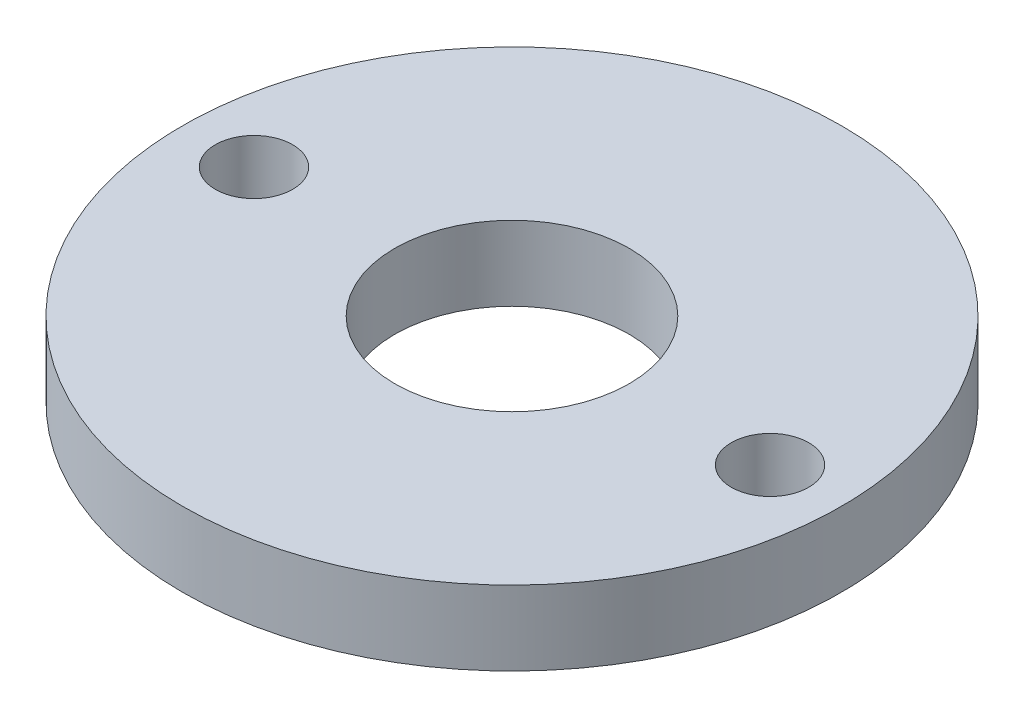
SolidWorks part; units mm, degrees
ref_plane "Front Plane" through (0, 0, 0) normal (0, 0, 1) x (1, 0, 0)
ref_plane "Top Plane" through (0, 0, 0) normal (0, 1, 0) x (1, 0, 0)
ref_plane "Right Plane" through (0, 0, 0) normal (1, 0, 0) x (0, 0, -1)
sketch "Sketch1" plane through (0, 0, 0) normal (0, 1, 0) x (1, 0, 0)
  line L0 (11, 0) -> (-11, 0) construction
  circle A0 centre (0, 0) radius 14.05
  circle A1 centre (0, 0) radius 5
  circle A2 centre (11, 0) radius 1.65
  circle A3 centre (-11, 0) radius 1.65
  point P11 (0, 0)
  dimension "D1" = 28.1
  dimension "D2" = 10
  dimension "D4" = 3.3
  dimension "D3" = 22
extrude "Boss-Extrude1" add sketch "Sketch1" along normal blind 3.175
